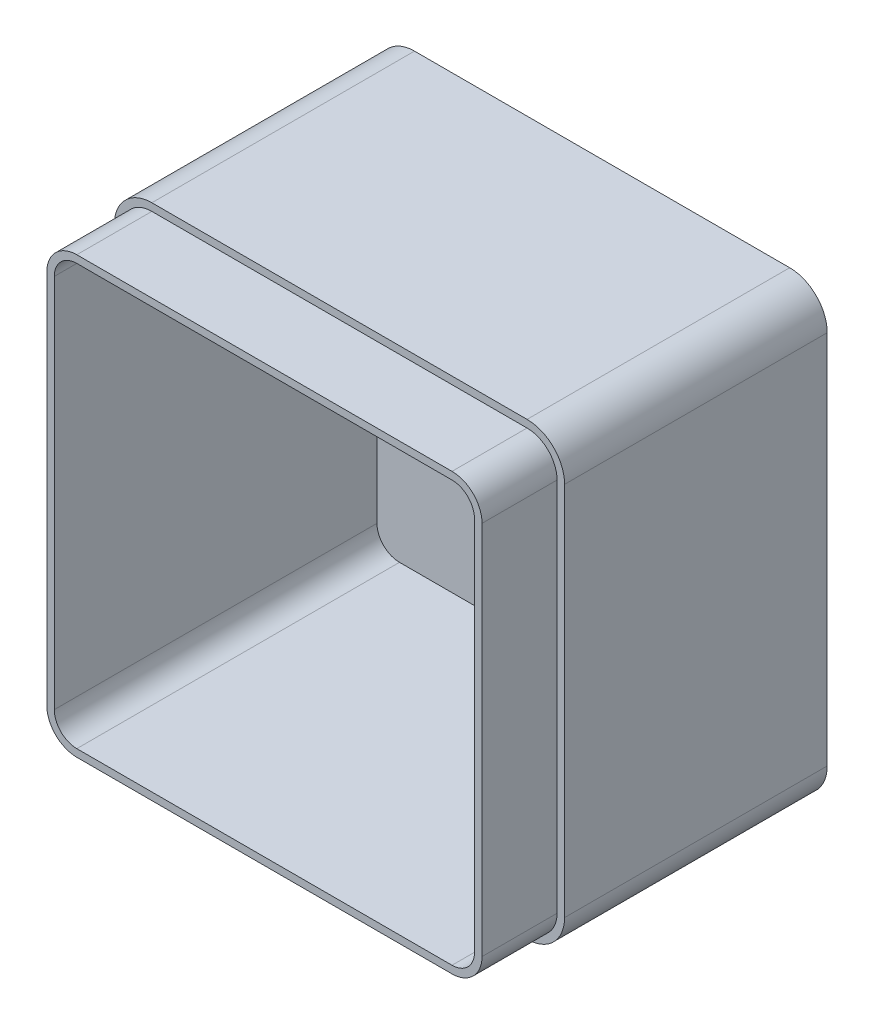
SolidWorks part; units mm, degrees
ref_plane "Front Plane" through (0, 0, 0) normal (0, 0, 1) x (1, 0, 0)
ref_plane "Top Plane" through (0, 0, 0) normal (0, 1, 0) x (1, 0, 0)
ref_plane "Right Plane" through (0, 0, 0) normal (1, 0, 0) x (0, 0, -1)
sketch "Sketch1" plane through (0, 0, 0) normal (0, 0, 1) x (1, 0, 0)
  line L1 (0, 0) -> (120, 0)
  line L2 (0, 0) -> (0, 120)
  line L3 (0, 120) -> (120, 120)
  line L4 (120, 0) -> (120, 120)
  dimension "D1" = 120
  dimension "D2" = 120
extrude "Boss-Extrude1" add sketch "Sketch1" along normal blind 90
fillet "Fillet1" radius 10 4 edges at (0, 0, 45) (0, 120, 45) (120, 0, 45) (120, 120, 45)
shell "Shell1" thickness 4
sketch "Sketch2" plane through (0, 0, 90) normal (0, 0, 1) x (1, 0, 0)
  line L0 (2, 110) -> (2, 10)
  line L1 (10, 2) -> (110, 2)
  line L2 (118, 10) -> (118, 110)
  line L3 (110, 118) -> (10, 118)
  line L4 (0, 110) -> (0, 10)
  line L5 (10, 0) -> (110, 0)
  line L6 (120, 10) -> (120, 110)
  line L7 (110, 120) -> (10, 120)
  line L8 (0, 110) -> (0, 10)
  line L9 (10, 0) -> (110, 0)
  line L10 (120, 10) -> (120, 110)
  line L11 (110, 120) -> (10, 120)
  arc A0 (2, 10) -> (10, 2) centre (10, 10) ccw
  arc A1 (110, 2) -> (118, 10) centre (110, 10) ccw
  arc A2 (118, 110) -> (110, 118) centre (110, 110) ccw
  arc A3 (10, 118) -> (2, 110) centre (10, 110) ccw
  arc A4 (0, 10) -> (10, 0) centre (10, 10) ccw
  arc A5 (110, 0) -> (120, 10) centre (110, 10) ccw
  arc A6 (120, 110) -> (110, 120) centre (110, 110) ccw
  arc A7 (10, 120) -> (0, 110) centre (10, 110) ccw
  arc A8 (0, 10) -> (10, 0) centre (10, 10) ccw
  arc A9 (110, 0) -> (120, 10) centre (110, 10) ccw
  arc A10 (120, 110) -> (110, 120) centre (110, 110) ccw
  arc A11 (10, 120) -> (0, 110) centre (10, 110) ccw
  dimension "D1" = 0
  dimension "D2" = 2
extrude "Cut-Extrude2" cut sketch "Sketch2" against normal blind 20
